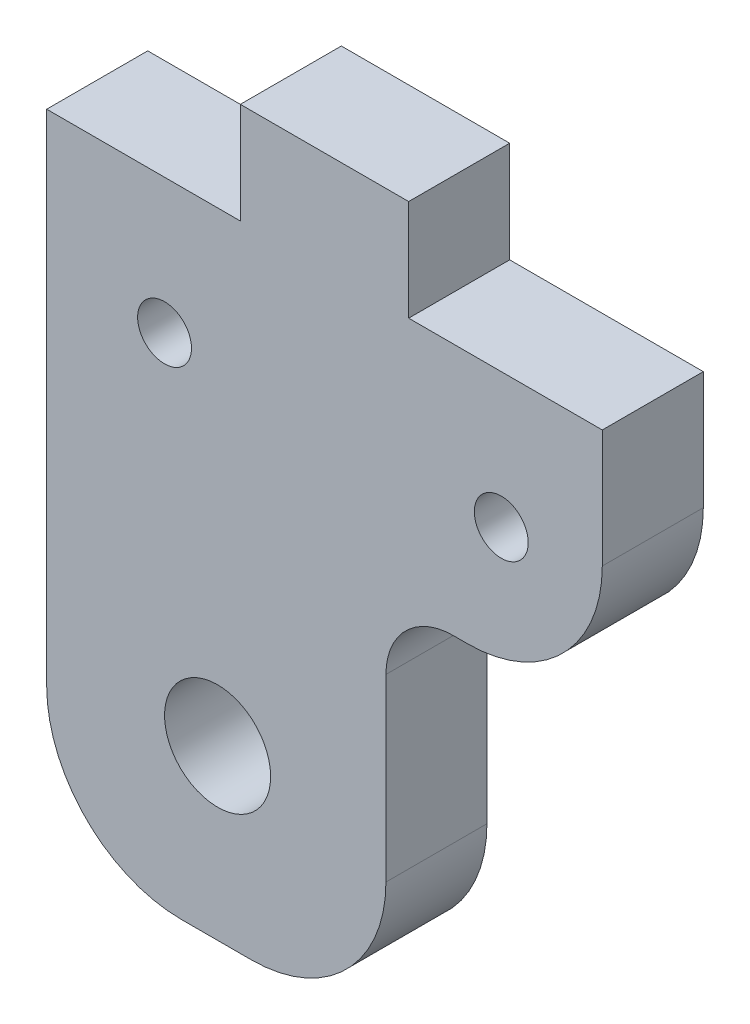
SolidWorks part; units mm, degrees
material "MDF"
ref_plane "Plano frontal" through (0, 0, 0) normal (0, 0, 1) x (1, 0, 0)
ref_plane "Plano superior" through (0, 0, 0) normal (0, 1, 0) x (1, 0, 0)
ref_plane "Plano direito" through (0, 0, 0) normal (1, 0, 0) x (0, 0, -1)
sketch "Esboço1" plane through (0, 0, 0) normal (0, 0, 1) x (1, 0, 0)
  line L5 (0, 0) -> (42, 0)
  line L10 (9.3685, -29.76) -> (13.2251, -47.9036) construction
  line L11 (13.2251, -47.9036) -> (18.3114, -46.8225) construction
  line L12 (18.3114, -46.8225) -> (19.15, -27.6808) construction
  line L13 (19.15, -27.6808) -> (9.3685, -29.76) construction
  line L14 (42, 0) -> (42, -45)
  line L15 (42, -45) -> (0, -45)
  line L16 (0, -45) -> (0, 0)
  line L17 (21, 0) -> (21, -45) construction
  line L18 (19.15, -27.6808) -> (13.2251, -47.9036) construction
  line L19 (19.15, -27.6808) -> (12.0789, -34.7519) construction
  line L20 (12.0789, -34.7519) -> (25.1951, -47.868) construction
  line L21 (25.1951, -47.868) -> (28.872, -44.1911) construction
  line L22 (16, -8) -> (13.2251, -47.9036) construction
  line L25 (16, -8) -> (36, -8) construction
  line L27 (29.15, -45) -> (29.15, -15)
  line L47 (30.5, 6) -> (20.5, 6)
  line L48 (30.5, 6) -> (30.5, 0)
  line L49 (30.5, 0) -> (20.5, 0)
  line L50 (20.5, 6) -> (20.5, 0)
  line L51 (9, -3.4633) -> (42, -3.4633) construction
  line L52 (30.5, 3) -> (20.5, 3) construction
  line L54 (6, -39) -> (0, -39)
  line L56 (6, -39) -> (6, -29)
  line L60 (6, -29) -> (0, -29)
  line L61 (0, -39) -> (0, -29)
  line L62 (6, -39) -> (0, -29) construction
  line L63 (6, -29) -> (0, -39) construction
  line L64 (29.15, -15) -> (42, -15)
  line L65 (0, -19) -> (9, -19)
  line L66 (9, -19) -> (9, 0)
  circle A0 centre (19.15, -27.6808) radius 3.15
  circle A1 centre (19.15, -27.6808) radius 22.85 construction
  circle A3 centre (36, -8) radius 1.6
  circle A4 centre (16, -8) radius 1.6
  circle A15 centre (36, -8) radius 3 construction
  circle A16 centre (19.15, -27.6808) radius 10 construction
  point P5 (42, -27.6808)
  point P8 (3, -34)
  point P11 (16, -27.6808)
  point P25 (22.3, -27.6808)
  point P31 (25.5, 3)
  point P40 (25.5, -3.4633)
  dimension "D3" = 6.3
  dimension "D6" = 10
  dimension "D11" = 10
  dimension "D19" = 6
  dimension "D18" = 8
  dimension "D10" = 6
  dimension "D21" = 6
  dimension "D23" = 20
  dimension "D15" = 6
  dimension "D13" = 3.2
  dimension "D16" = 16
  dimension "D4" = 19.16
  dimension "D5" = 5.2
  dimension "D7" = 12
  dimension "D8" = 40
  dimension "D9" = 16
  dimension "D12" = 45
  dimension "D14" = 34
  dimension "D17" = 20
  dimension "D20" = 10
  dimension "D22" = 45
  dimension "D24" = 7
  dimension "D25" = 10
  dimension "D26" = 10
  dimension "D27" = 9
extrude "Ressalto-extrusão1" add sketch "Esboço1" along normal blind 6
fillet "Filete3" radius 4 1 edges at (29.15, -15, 3)
sketch "Esboço2" plane through (0, 0, 6) normal (0, 0, 1) x (1, 0, 0)
  line L0 (29.15, -45) -> (0, -45) construction
  line L1 (0, -19) -> (9, -19)
  line L2 (0, -19) -> (0, -45)
  line L3 (0, -45) -> (9, -45)
  line L4 (9, -19) -> (9, -45)
  line L7 (9, -37.6808) -> (29.15, -37.6808)
  line L8 (9, -37.6808) -> (9, -45)
  line L9 (9, -45) -> (29.15, -45)
  line L10 (29.15, -37.6808) -> (29.15, -45)
  circle A1 centre (19.15, -27.6808) radius 3.15 construction
  line M4 (29.15, -45) -> (29.15, -19)
  line M15 (9, -19) -> (0, -19)
  line M16 (0, -19) -> (0, -29)
  line M17 (0, -29) -> (6, -29)
  line M18 (6, -29) -> (6, -39)
  line M19 (6, -39) -> (0, -39)
  line M20 (0, -39) -> (0, -45)
  line M21 (0, -45) -> (29.15, -45)
  dimension "D1" = 10
extrude "Corte-extrusão1" cut sketch "Esboço2" against normal blind 10 contours L4 M15 M16 M17 M18 M19 M20 M21 | L7 L4 M21 M4
fillet "Filete2" radius 8 3 edges at (42, -15, 3) (29.15, -37.6808, 3) (9, -37.6808, 3)
